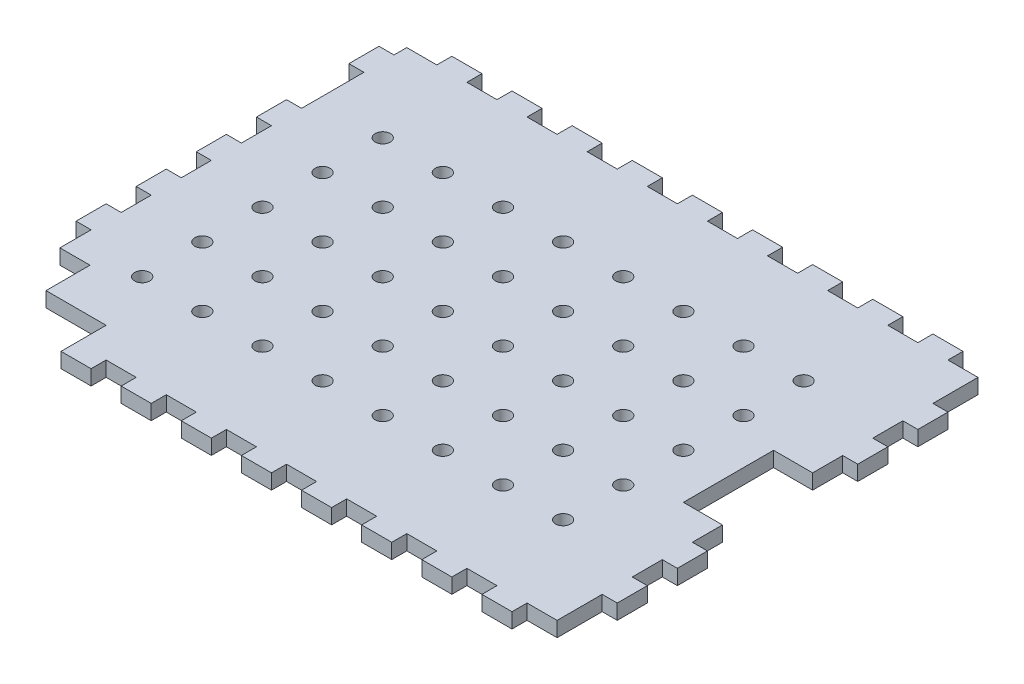
SolidWorks part; units mm, degrees
material "Balsa"
ref_plane "Alzado" through (0, 0, 0) normal (0, 0, 1) x (1, 0, 0)
ref_plane "Planta" through (0, 0, 0) normal (0, 1, 0) x (1, 0, 0)
ref_plane "Vista lateral" through (0, 0, 0) normal (1, 0, 0) x (0, 0, -1)
sketch "Croquis1" plane through (0, 0, 0) normal (0, 1, 0) x (1, 0, 0)
  line L1 (0, 0) -> (200, 0)
  line L2 (0, 0) -> (0, 150)
  line L3 (0, 150) -> (200, 150)
  line L4 (200, 0) -> (200, 150)
  line L9 (0, 150) -> (5, 150)
  line L10 (0, 150) -> (0, 140.75)
  line L11 (0, 140.75) -> (5, 140.75)
  line L12 (5, 150) -> (5, 140.75)
  line L28 (0, 80) -> (5, 80)
  line L29 (0, 130.75) -> (5, 130.75)
  line L30 (0, 130.75) -> (0, 110)
  line L31 (0, 110) -> (5, 110)
  line L32 (5, 130.75) -> (5, 110)
  line L33 (0, 100) -> (5, 100)
  line L34 (0, 100) -> (0, 90)
  line L35 (0, 90) -> (5, 90)
  line L36 (5, 100) -> (5, 90)
  line L37 (0, 9.25) -> (5, 9.25)
  line L38 (5, 0) -> (5, 9.25)
  line L39 (0, 0) -> (5, 0)
  line L40 (0, 0) -> (0, 9.25)
  line L41 (0, 40) -> (5, 40)
  line L42 (5, 19.25) -> (5, 40)
  line L43 (0, 19.25) -> (5, 19.25)
  line L44 (0, 19.25) -> (0, 40)
  line L45 (0, 60) -> (5, 60)
  line L46 (5, 50) -> (5, 60)
  line L47 (0, 50) -> (5, 50)
  line L48 (0, 50) -> (0, 60)
  line L49 (5, 70) -> (5, 80)
  line L50 (0, 70) -> (5, 70)
  line L51 (0, 70) -> (0, 80)
  line L52 (45, 0) -> (45, 5)
  line L53 (0, 0) -> (15, 0)
  line L54 (0, 0) -> (0, 5)
  line L55 (0, 5) -> (15, 5)
  line L56 (15, 0) -> (15, 5)
  line L57 (25, 0) -> (35, 0)
  line L58 (25, 0) -> (25, 5)
  line L59 (25, 5) -> (35, 5)
  line L60 (35, 0) -> (35, 5)
  line L61 (45, 0) -> (55, 0)
  line L62 (55, 0) -> (55, 5)
  line L63 (45, 5) -> (55, 5)
  line L64 (65, 0) -> (65, 5)
  line L65 (65, 0) -> (75, 0)
  line L66 (75, 0) -> (75, 5)
  line L67 (65, 5) -> (75, 5)
  line L68 (85, 0) -> (85, 5)
  line L69 (85, 0) -> (95, 0)
  line L70 (95, 0) -> (95, 5)
  line L71 (85, 5) -> (95, 5)
  line L72 (105, 0) -> (105, 5)
  line L73 (105, 0) -> (115, 0)
  line L74 (115, 0) -> (115, 5)
  line L75 (105, 5) -> (115, 5)
  line L76 (125, 0) -> (125, 5)
  line L77 (125, 0) -> (135, 0)
  line L78 (135, 0) -> (135, 5)
  line L79 (125, 5) -> (135, 5)
  line L80 (145, 0) -> (145, 5)
  line L81 (145, 0) -> (155, 0)
  line L82 (155, 0) -> (155, 5)
  line L83 (145, 5) -> (155, 5)
  line L84 (165, 0) -> (165, 5)
  line L85 (200, 0) -> (185, 0)
  line L86 (200, 0) -> (200, 5)
  line L87 (200, 5) -> (185, 5)
  line L88 (185, 0) -> (185, 5)
  line L89 (165, 5) -> (175, 5)
  line L90 (175, 0) -> (175, 5)
  line L91 (165, 0) -> (175, 0)
  line L92 (200, 100) -> (200, 90)
  line L93 (200, 145) -> (185, 145)
  line L94 (185, 150) -> (185, 145)
  line L95 (200, 150) -> (185, 150)
  line L96 (200, 150) -> (200, 145)
  line L97 (165, 150) -> (175, 150)
  line L98 (175, 150) -> (175, 145)
  line L99 (165, 145) -> (175, 145)
  line L100 (165, 150) -> (165, 145)
  line L101 (145, 150) -> (155, 150)
  line L102 (155, 150) -> (155, 145)
  line L103 (145, 145) -> (155, 145)
  line L104 (145, 150) -> (145, 145)
  line L105 (125, 150) -> (135, 150)
  line L106 (135, 150) -> (135, 145)
  line L107 (125, 145) -> (135, 145)
  line L108 (125, 150) -> (125, 145)
  line L109 (105, 150) -> (115, 150)
  line L110 (115, 150) -> (115, 145)
  line L111 (105, 145) -> (115, 145)
  line L112 (105, 150) -> (105, 145)
  line L113 (85, 150) -> (95, 150)
  line L114 (95, 150) -> (95, 145)
  line L115 (85, 145) -> (95, 145)
  line L116 (85, 150) -> (85, 145)
  line L117 (65, 150) -> (75, 150)
  line L118 (75, 150) -> (75, 145)
  line L119 (65, 145) -> (75, 145)
  line L120 (65, 150) -> (65, 145)
  line L121 (45, 150) -> (55, 150)
  line L122 (55, 150) -> (55, 145)
  line L123 (45, 145) -> (55, 145)
  line L124 (45, 150) -> (45, 145)
  line L125 (25, 145) -> (35, 145)
  line L126 (35, 150) -> (35, 145)
  line L127 (25, 150) -> (35, 150)
  line L128 (25, 150) -> (25, 145)
  line L129 (0, 145) -> (15, 145)
  line L130 (15, 150) -> (15, 145)
  line L131 (0, 150) -> (15, 150)
  line L132 (0, 150) -> (0, 145)
  line L133 (200, 150) -> (195, 150)
  line L134 (200, 150) -> (200, 130)
  line L135 (200, 130) -> (195, 130)
  line L136 (195, 150) -> (195, 130)
  line L137 (200, 120) -> (195, 120)
  line L138 (200, 120) -> (200, 110)
  line L139 (200, 110) -> (195, 110)
  line L140 (195, 120) -> (195, 110)
  line L141 (200, 100) -> (195, 100)
  line L142 (195, 100) -> (195, 90)
  line L143 (200, 90) -> (195, 90)
  line L144 (200, 80) -> (200, 70)
  line L145 (200, 80) -> (195, 80)
  line L146 (195, 80) -> (195, 70)
  line L147 (200, 70) -> (195, 70)
  line L148 (200, 60) -> (200, 50)
  line L149 (200, 60) -> (195, 60)
  line L150 (195, 60) -> (195, 50)
  line L151 (200, 50) -> (195, 50)
  line L152 (200, 40) -> (200, 30)
  line L153 (200, 40) -> (195, 40)
  line L154 (195, 40) -> (195, 30)
  line L155 (200, 30) -> (195, 30)
  line L157 (200, 0) -> (195, 0)
  line L158 (200, 0) -> (200, 20)
  line L159 (200, 20) -> (195, 20)
  line L160 (195, 0) -> (195, 20)
  dimension "D1" = 150
  dimension "D2" = 200
  dimension "D3" = 9.25
  dimension "D4" = 5
  dimension "D5" = 10
  dimension "D6" = 20.75
  dimension "D7" = 10
  dimension "D8" = 10
  dimension "D10" = 5
  dimension "D11" = 15
  dimension "D12" = 10
  dimension "D13" = 10
  dimension "D15" = 5
  dimension "D16" = 15
  dimension "D17" = 2
  dimension "D18" = 20
  dimension "D19" = 5
  dimension "D20" = 10
  dimension "D21" = 5
  dimension "D22" = 10
  dimension "D24" = 5
  dimension "D25" = 20
  dimension "D9" = 2
  dimension "D14" = 7
  dimension "D23" = 5
extrude "Saliente-Extruir1" add sketch "Croquis1" along normal blind 5 contours L87 L160 L159 L4 L155 L154 L153 L151 L150 L149 L147 L146 L145 L143 L142 L141 L139 L140 L137 L135 L136 L93 L94 L3 L98 L99 L100 L102 L103 L104 L106 L107 L108 L110 L111 L112 L114 L115 L116 L118 L119
sketch "Croquis2" plane through (0, 5, 0) normal (0, 1, 0) x (1, 0, 0)
  line L0 (5, 29.625) -> (5, 19.25)
  line L9 (5, 19.25) -> (0, 19.25)
  line L11 (35, 5) -> (35, 15)
  line L12 (35, 15) -> (15, 15)
  line L14 (5, 5) -> (15, 5)
  line L16 (5, 29.625) -> (15, 29.625)
  line L17 (15, 15) -> (15, 29.625)
  line L18 (0, 19.25) -> (0, 9.25)
  line L19 (0, 9.25) -> (5, 9.25)
  line L20 (5, 9.25) -> (5, 5)
  line L21 (15, 5) -> (15, 0)
  line L22 (15, 0) -> (25, 0)
  line L23 (25, 0) -> (25, 5)
  line L24 (25, 0) -> (25, 5) construction
  line L25 (25, 5) -> (35, 5)
  line L26 (195, 90) -> (200, 90)
  line L27 (195, 90) -> (182, 90)
  line L29 (195, 60) -> (182, 60)
  line L30 (182, 90) -> (182, 60)
  line L31 (200, 90) -> (200, 80)
  line L32 (200, 80) -> (195, 80)
  line L33 (195, 80) -> (195, 70)
  line L34 (195, 70) -> (200, 70)
  line L35 (200, 70) -> (200, 60)
  line L36 (200, 60) -> (195, 60)
  circle A0 centre (27, 115) radius 2.5
  circle A1 centre (47, 115) radius 2.5
  circle A2 centre (67, 115) radius 2.5
  circle A3 centre (87, 115) radius 2.5
  circle A4 centre (107, 115) radius 2.5
  circle A5 centre (127, 115) radius 2.5
  circle A6 centre (147, 115) radius 2.5
  circle A7 centre (167, 115) radius 2.5
  circle A8 centre (47, 95) radius 2.5
  circle A9 centre (67, 95) radius 2.5
  circle A10 centre (87, 95) radius 2.5
  circle A11 centre (107, 95) radius 2.5
  circle A12 centre (127, 95) radius 2.5
  circle A13 centre (147, 95) radius 2.5
  circle A14 centre (167, 95) radius 2.5
  circle A15 centre (47, 75) radius 2.5
  circle A16 centre (67, 75) radius 2.5
  circle A17 centre (87, 75) radius 2.5
  circle A18 centre (107, 75) radius 2.5
  circle A19 centre (127, 75) radius 2.5
  circle A20 centre (147, 75) radius 2.5
  circle A21 centre (167, 75) radius 2.5
  circle A22 centre (47, 55) radius 2.5
  circle A23 centre (67, 55) radius 2.5
  circle A24 centre (87, 55) radius 2.5
  circle A25 centre (107, 55) radius 2.5
  circle A26 centre (127, 55) radius 2.5
  circle A27 centre (147, 55) radius 2.5
  circle A28 centre (167, 55) radius 2.5
  circle A29 centre (47, 35) radius 2.5
  circle A30 centre (67, 35) radius 2.5
  circle A31 centre (87, 35) radius 2.5
  circle A32 centre (107, 35) radius 2.5
  circle A33 centre (127, 35) radius 2.5
  circle A34 centre (147, 35) radius 2.5
  circle A35 centre (167, 35) radius 2.5
  circle A36 centre (27, 95) radius 2.5
  circle A37 centre (27, 75) radius 2.5
  circle A38 centre (27, 55) radius 2.5
  circle A39 centre (27, 35) radius 2.5
  dimension "D11" = 5
  dimension "D1" = 30
  dimension "D2" = 13
  dimension "D3" = 8
  dimension "D4" = 5
  dimension "D6" = 10
  dimension "D7" = 24.625
extrude "Cortar-Extruir1" cut sketch "Croquis2" against normal blind 10
